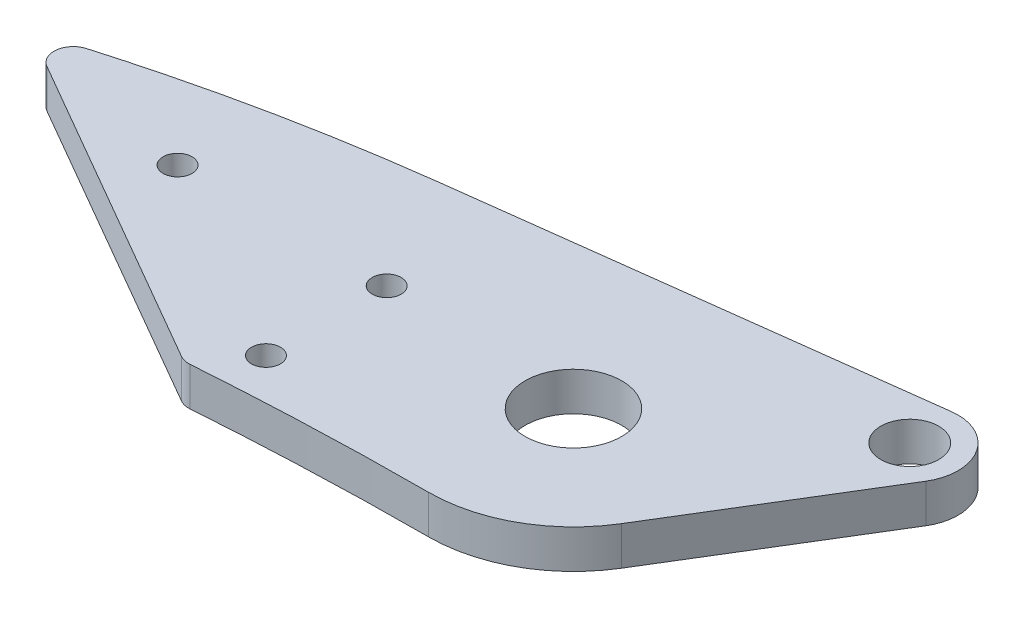
SolidWorks part; units mm, degrees
ref_plane "Front Plane" through (0, 0, 0) normal (0, 0, 1) x (1, 0, 0)
ref_plane "Top Plane" through (0, 0, 0) normal (0, 1, 0) x (1, 0, 0)
ref_plane "Right Plane" through (0, 0, 0) normal (1, 0, 0) x (0, 0, -1)
sketch "Sketch1" plane through (0, 0, 0) normal (0, 1, 0) x (1, 0, 0)
  line L0 (0, 0) -> (-143.2011, 0) construction
  line L1 (0, 0) -> (10.6066, 10.6066) construction
  line L2 (0, 0) -> (15, 0) construction
  line L3 (-143.2011, 0) -> (-143.2011, -44.6479) construction
  line L4 (-143.2011, -44.6479) -> (0, 0) construction
  line L5 (-150.2325, -43.7465) -> (-144.1674, -51.5547)
  circle A1 centre (0, 0) radius 15
  circle A3 centre (-143.2011, -44.6479) radius 5 construction
  circle A4 centre (-143.2011, -44.6479) radius 1.5
  spline S0 degree 3 poles (0, -15) (-49.2112, -15) (-112.5778, -27.017) (-144.1674, -51.5547) knots 0 0 0 0 1 1 1 1
  spline S1 degree 3 poles (0, 15) (-53.3333, 15) (-97.5832, -2.8503) (-150.2325, -43.7465) knots 0 0 0 0 1 1 1 1
  dimension "D1" = 150
  dimension "D2" = 30
  dimension "D4" = 9.887
  dimension "D7" = 200
  dimension "D8" = 160
  dimension "D3" = 10
  dimension "D6" = 3
  dimension "D9" = 120
  dimension "D10" = 147.6335
  dimension "D5" = 45
extrude "Boss-Extrude4" add sketch "Sketch1" along normal blind 4
sketch "Sketch2" plane through (0, 0, 0) normal (0, -1, 0) x (1, 0, 0)
  line L0 (15, 0) -> (0, 0) construction
  line L1 (0, 0) -> (20.4788, -14.3394) construction
  line L2 (12.8003, 7.82) -> (24.7456, -11.7327)
  line L3 (19.8504, -19.2998) -> (-27.3151, -13.3251)
  line L4 (-143.2011, 44.6479) -> (0, 0) construction
  circle A0 centre (0, 0) radius 15
  circle A2 centre (20.4788, -14.3394) radius 3
  arc A3 (24.7456, -11.7327) -> (19.8504, -19.2998) centre (20.4788, -14.3394) cw
  spline S0 degree 3 poles (0, -15) (-53.3333, -15) (-97.5832, 2.8503) (-150.2325, 43.7465) knots 0 0 0 0 1 1 1 1 construction
  dimension "D3" = 5
  dimension "D4" = 30
  dimension "D5" = 6
  dimension "D1" = 35
  dimension "D2" = 25
  dimension "D6" = 162.317
extrude "Boss-Extrude6" add sketch "Sketch2" against normal blind 4
sketch "Sketch6" plane through (0, 4, 0) normal (0, 1, 0) x (1, 0, 0)
  line L0 (-57.046, 7.2081) -> (12.8919, 7.668)
  line L1 (12.8919, 7.668) -> (7.2723, 26.2924)
  line L2 (7.2723, 26.2924) -> (-49.3026, 23.0614)
  line L3 (-49.3026, 23.0614) -> (-57.046, 7.2081)
  arc A0 (0, -15) -> (12.8003, -7.82) centre (0, 0) ccw construction
  spline S0 degree 3 poles (-27.3151, 13.3251) (-69.1117, 8.0305) (-106.8162, -10.0222) (-150.2325, -43.7465) knots 0.175368 0.175368 0.175368 0.175368 1 1 1 1 construction
extrude "Cut-Extrude2" [suppressed] cut sketch "Sketch6" against normal blind 5
fillet "Fillet3" [suppressed] radius 1
sketch "Sketch8" plane through (0, 4, 0) normal (0, 1, 0) x (1, 0, 0)
  line L0 (-61.9301, 5.7332) -> (-24.4288, -15.9183)
  line L1 (-61.9301, 5.7332) -> (-181.3906, 23.0066)
  line L2 (-181.3906, 23.0066) -> (-136.2242, -112.6868)
  line L3 (-136.2242, -112.6868) -> (-81.4186, -101.3468)
  line L4 (-81.4186, -101.3468) -> (-24.4288, -15.9183)
  line L5 (0, 28.3515) -> (0, -37.896) construction
  spline S0 degree 3 poles (0, -15) (-49.2112, -15) (-112.5778, -27.017) (-144.1674, -51.5547) knots 0 0 0 0 1 1 1 1 construction
  spline S1 degree 3 poles (-27.3151, 13.3251) (-69.1117, 8.0305) (-106.8162, -10.0222) (-150.2325, -43.7465) knots 0.175368 0.175368 0.175368 0.175368 1 1 1 1 construction
  dimension "D1" = 26
  dimension "D2" = 60
extrude "Cut-Extrude4" cut sketch "Sketch8" against normal through all
fillet "Fillet4" radius 2 2 edges at (-24.4288, 2, 15.9183) (-61.9301, 2, -5.7332)
sketch "Sketch7" plane through (0, 4, 0) normal (0, 1, 0) x (1, 0, 0)
  line L1 (-42.3267, 1.3433) -> (-20.676, -11.1567) construction
  line L5 (-20.676, -11.1567) -> (-20.676, 1.3433) construction
  line L6 (-20.676, 1.3433) -> (-42.3267, 1.3433) construction
  line L7 (-24.9605, -15.6112) -> (-57.9345, 3.4263) construction
  circle A0 centre (0, 0) radius 5
  circle A4 centre (-42.3267, 1.3433) radius 1.5
  circle A8 centre (-20.676, -11.1567) radius 1.5
  circle A9 centre (-20.676, 1.3433) radius 1.5
  dimension "D1" = 10
  dimension "D3" = 25
  dimension "D4" = 6
  dimension "D2" = 3
extrude "Cut-Extrude3" cut sketch "Sketch7" against normal blind 10
